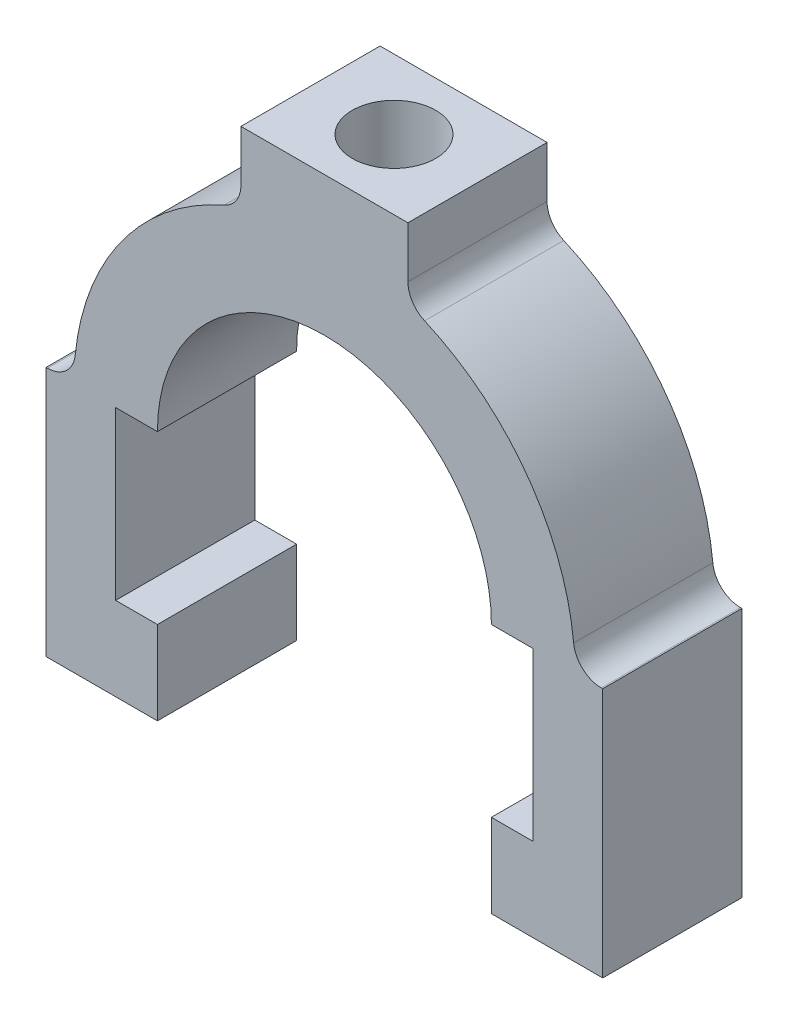
SolidWorks part; units mm, degrees
material "1060 Alloy"
ref_plane "Front Plane" through (0, 0, 0) normal (0, 0, 1) x (1, 0, 0)
ref_plane "Top Plane" through (0, 0, 0) normal (0, 1, 0) x (1, 0, 0)
ref_plane "Right Plane" through (0, 0, 0) normal (1, 0, 0) x (0, 0, -1)
sketch "Sketch1" plane through (0, 0, 0) normal (0, 0, 1) x (1, 0, 0)
  line L1 (0, 0) -> (80, 0)
  line L2 (0, 0) -> (0, 80)
  line L3 (0, 80) -> (80, 80)
  line L4 (80, 0) -> (80, 80)
  dimension "D1" = 80
  dimension "D2" = 80
extrude "Boss-Extrude1" add sketch "Sketch1" against normal blind 20
sketch "Sketch2" plane through (0, 0, 0) normal (0, 0, 1) x (1, 0, 0)
  line L0 (40, -1000) -> (40, 49000) construction
  line L1 (0, 0) -> (80, 0) construction
  line L2 (16, 0) -> (64, 0)
  line L3 (64, 0) -> (64, 12)
  line L4 (64, 12) -> (70, 12)
  line L5 (70, 12) -> (70, 36)
  line L6 (70, 36) -> (10, 36)
  line L7 (16, 0) -> (16, 12)
  line L8 (16, 12) -> (10, 12)
  line L9 (10, 12) -> (10, 36)
  point P5 (40, 0)
  point P13 (40, 0)
  point P16 (40, 36)
  dimension "D1" = 16
  dimension "D2" = 6
  dimension "D3" = 36
  dimension "D4" = 12
extrude "Cut-Extrude1" cut sketch "Sketch2" against normal through all
sketch "Sketch3" plane through (0, 0, 0) normal (0, 0, 1) x (1, 0, 0)
  line L0 (70, 36) -> (10, 36) construction
  circle A0 centre (40, 36) radius 24
  dimension "D1" = 24
extrude "Cut-Extrude2" cut sketch "Sketch3" against normal through all
sketch "Sketch4" plane through (0, 0, 0) normal (0, 0, 1) x (1, 0, 0)
  line L0 (-960, 36) -> (49040, 36) construction
  line L2 (4, 36) -> (0, 36)
  line L3 (0, 80) -> (0, 0) construction
  line L4 (0, 36) -> (0, 80)
  line L5 (0, 80) -> (28, 80)
  line L6 (80, 80) -> (0, 80) construction
  line L7 (28, 80) -> (28, 69.9411)
  line L8 (40, -964) -> (40, 49036) construction
  line L10 (76, 36) -> (80, 36)
  line L11 (80, 36) -> (80, 80)
  line L12 (80, 80) -> (52, 80)
  line L13 (52, 80) -> (52, 69.9411)
  arc A0 (76, 36) -> (52, 69.9411) centre (40, 36) ccw
  arc A1 (64, 36) -> (16, 36) centre (40, 36) ccw construction
  arc A2 (28, 69.9411) -> (4, 36) centre (40, 36) ccw
  dimension "D1" = 36
  dimension "D2" = 28
extrude "Cut-Extrude3" cut sketch "Sketch4" against normal through all
sketch "Sketch5" plane through (0, 80, 0) normal (0, 1, 0) x (1, 0, 0)
  line L0 (40, -1000) -> (40, 49000) construction
  line L1 (52, 0) -> (28, 0) construction
  line L2 (-948, 10) -> (49052, 10) construction
  line L3 (52, 20) -> (52, 0) construction
  circle A0 centre (40, 10) radius 6
  point P5 (40, 0)
  point P10 (52, 10)
  dimension "D1" = 12
extrude "Cut-Extrude4" cut sketch "Sketch5" against normal through all
fillet "Fillet1" radius 4 4 edges at (4, 36, -10) (28, 69.9411, -10) (76, 36, -10) (52, 69.9411, -10)
